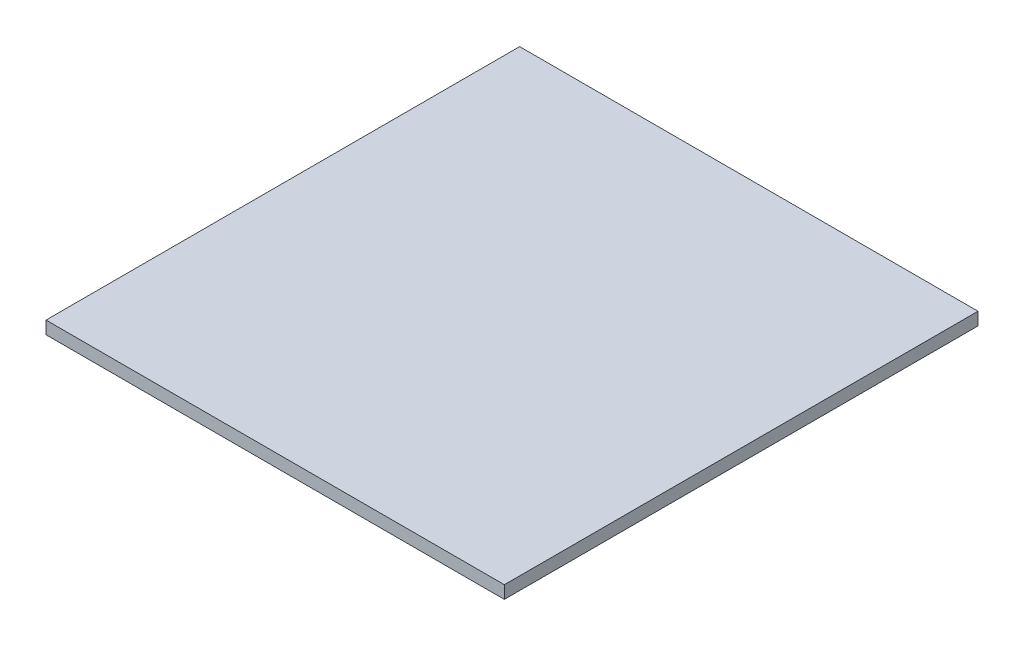
SolidWorks part; units mm, degrees
ref_plane "Front Plane" through (0, 0, 0) normal (0, 0, 1) x (1, 0, 0)
ref_plane "Top Plane" through (0, 0, 0) normal (0, 1, 0) x (1, 0, 0)
ref_plane "Right Plane" through (0, 0, 0) normal (1, 0, 0) x (0, 0, -1)
sketch "Sketch1" plane through (0, 0, 0) normal (0, 1, 0) x (1, 0, 0)
  line L1 (0, 0) -> (571.5, 0)
  line L2 (0, 0) -> (0, 590.55)
  line L3 (0, 590.55) -> (571.5, 590.55)
  line L4 (571.5, 0) -> (571.5, 590.55)
  dimension "D1" = 571.5
  dimension "D2" = 590.55
extrude "Boss-Extrude1" add sketch "Sketch1" along normal blind 15.875
